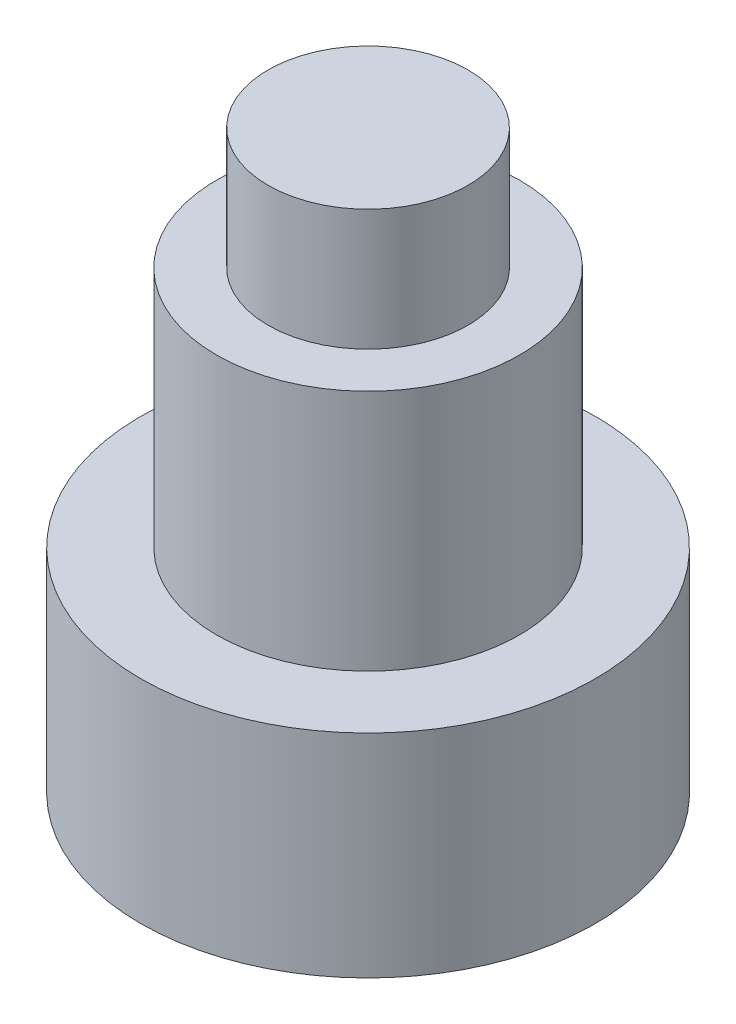
SolidWorks part; units mm, degrees
ref_plane "Front Plane" through (0, 0, 0) normal (0, 0, 1) x (1, 0, 0)
ref_plane "Top Plane" through (0, 0, 0) normal (0, 1, 0) x (1, 0, 0)
ref_plane "Right Plane" through (0, 0, 0) normal (1, 0, 0) x (0, 0, -1)
sketch "Sketch1" plane through (0, 0, 0) normal (0, 1, 0) x (1, 0, 0)
  circle A0 centre (0, 0) radius 3.75
extrude "Boss-Extrude1" add sketch "Sketch1" along normal blind 7.5
sketch "Sketch2" plane through (0, 7.5, 0) normal (0, 1, 0) x (1, 0, 0)
  circle A0 centre (0, 0) radius 2.5
  circle A1 centre (0, 0) radius 3.75
extrude "Cut-Extrude1" cut sketch "Sketch2" against normal blind 4
sketch "Sketch3" plane through (0, 7.5, 0) normal (0, 1, 0) x (1, 0, 0)
  circle A0 centre (0, 0) radius 1.65
extrude "Boss-Extrude2" add sketch "Sketch3" along normal blind 2
